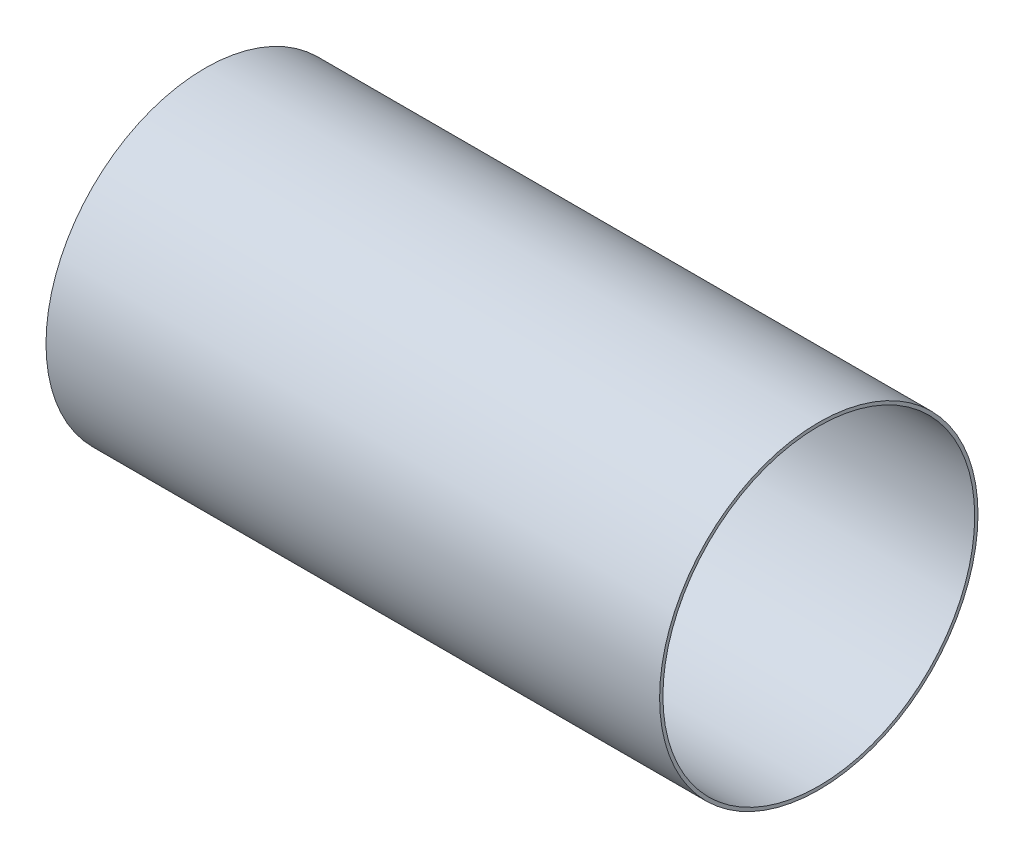
SolidWorks part; units mm, degrees
material "Thornel Mat VMA"
ref_plane "Front Plane" through (0, 0, 0) normal (0, 0, 1) x (1, 0, 0)
ref_plane "Top Plane" through (0, 0, 0) normal (0, 1, 0) x (1, 0, 0)
ref_plane "Right Plane" through (0, 0, 0) normal (1, 0, 0) x (0, 0, -1)
ref_axis "Axis1" through (88.99, 0, 0) along (-1, 0, 0)
sketch "Sketch1" plane through (0, 0, 0) normal (0, 0, 1) x (1, 0, 0)
  line L0 (88.99, 0) -> (-88.99, 0) construction
  line L1 (0, 9.6) -> (37, 9.6)
  line L2 (0, 9.6) -> (0, 9.4)
  line L3 (0, 9.4) -> (37, 9.4)
  line L4 (37, 9.6) -> (37, 9.4)
  dimension "D1" = 18.8
  dimension "D2" = 37
  dimension "D3" = 0.2
revolve "Revolve1" add sketch "Sketch1" angle 360 about axis through (88.99, 0, 0) along (-1, 0, 0)
